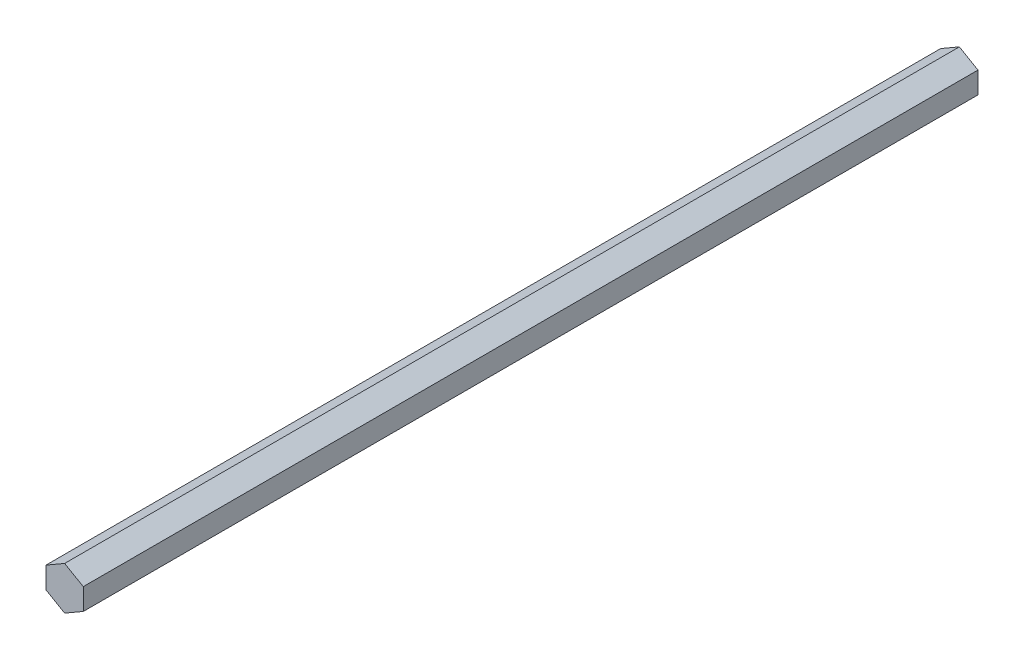
SolidWorks part; units mm, degrees
ref_plane "Front Plane" through (0, 0, 0) normal (0, 0, 1) x (1, 0, 0)
ref_plane "Top Plane" through (0, 0, 0) normal (0, 1, 0) x (1, 0, 0)
ref_plane "Right Plane" through (0, 0, 0) normal (1, 0, 0) x (0, 0, -1)
sketch "Sketch1" plane through (0, 0, 0) normal (0, 0, 1) x (1, 0, 0)
  line L0 (-6.35, 0) -> (6.35, 0) construction
  line L9 (0, 7.3323) -> (-6.35, 3.6662) construction
  line L10 (-6.35, 3.6662) -> (-6.35, -3.6662) construction
  line L11 (-6.35, -3.6662) -> (0, -7.3323) construction
  line L12 (0, -7.3323) -> (6.35, -3.6662) construction
  line L13 (6.35, -3.6662) -> (6.35, 3.6662) construction
  line L14 (6.35, 3.6662) -> (0, 7.3323) construction
  circle A3 centre (0, 0) radius 6.35 construction
  point P4 (0, 0)
  dimension "Width" = 12.7
sketch "Sketch2" plane through (0, 0, 0) normal (1, 0, 0) x (0, 0, -1)
  line L0 (152.4, 7.3323) -> (-152.4, 7.3323) construction
  point P3 (-137.795, 7.3323)
  point P4 (0, 7.3323)
  point P5 (137.795, 7.3323)
  dimension "Length" = 304.8
  dimension "D1" = 14.605
  dimension "D2" = 14.605
sketch "Sketch3" plane through (0, 0, 0) normal (0, 0, 1) x (1, 0, 0)
  line L1 (0, 7.3323) -> (6.35, 3.6662)
  line L2 (6.35, 3.6662) -> (6.35, -3.6662)
  line L3 (6.35, -3.6662) -> (0, -7.3323)
  line L4 (0, -7.3323) -> (-6.35, -3.6662)
  line L5 (-6.35, -3.6662) -> (-6.35, 3.6662)
  line L6 (-6.35, 3.6662) -> (0, 7.3323)
extrude "Boss-Extrude1" add sketch "Sketch3" along normal mid plane 304.8
equation "\"D1@Boss-Extrude1\" = \"Length@Sketch2\""
equation "\"D1@Sketch2\"=\"Width@Sketch1\"*1.15"
equation "\"D2@Sketch2\"=\"D1@Sketch2\""
